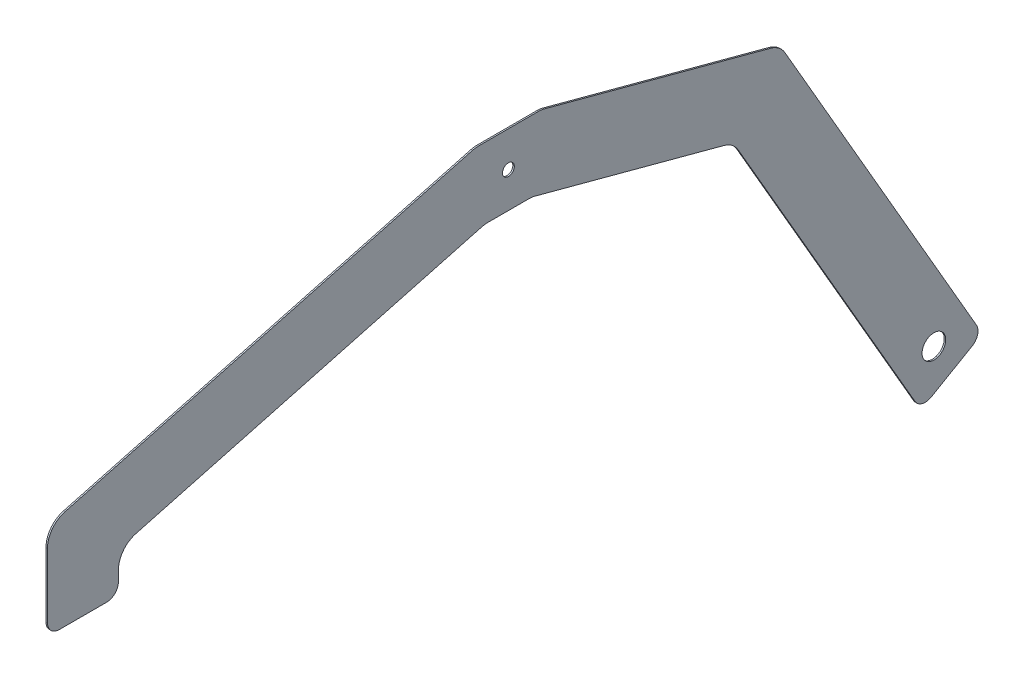
SolidWorks part; units mm, degrees
material "6061 Alloy"
ref_plane "Front Plane" through (0, 0, 0) normal (0, 0, 1) x (1, 0, 0)
ref_plane "Top Plane" through (0, 0, 0) normal (0, 1, 0) x (1, 0, 0)
ref_plane "Right Plane" through (0, 0, 0) normal (1, 0, 0) x (0, 0, -1)
sketch "Sketch1" plane through (0, 0, 0) normal (1, 0, 0) x (0, 0, -1)
  line L11 (-35.4319, 38.1) -> (35.4319, 38.1)
  line L12 (-25.4, -38.1) -> (25.4, -38.1)
  line L13 (0, -38.1) -> (0, 0) construction
  line L17 (-35.4319, 38.1) -> (-495.3, -85.1213)
  line L18 (-25.4, -38.1) -> (-419.1, -143.5916)
  line L19 (-495.3, -85.1213) -> (-495.3, -186.7213)
  line L20 (-495.3, -186.7213) -> (-419.1, -186.7213)
  line L21 (-419.1, -186.7213) -> (-419.1, -143.5916)
  line L22 (35.4319, 38.1) -> (291.9219, -30.6263)
  line L23 (25.4, -38.1) -> (241.7123, -96.0607)
  line L24 (241.7123, -96.0607) -> (443.2544, -445.1418)
  line L25 (443.2544, -445.1418) -> (509.2456, -407.0418)
  line L26 (509.2456, -407.0418) -> (291.9219, -30.6263)
  circle A0 centre (0, 0) radius 6.35
  circle A1 centre (457.2, -393.0963) radius 12.7
  point P9 (0, 0)
  point P18 (-457.2, -186.7213)
  dimension "D1" = 12.7
  dimension "D13" = 25.4
  dimension "D2" = 76.2
  dimension "D3" = 50.8
  dimension "D4" = 914.4
  dimension "D5" = 76.2
  dimension "D6" = 15
  dimension "D7" = 38.1
  dimension "D8" = 38.1
  dimension "D9" = 206.375
  dimension "D10" = 101.6
  dimension "D11" = 76.2
  dimension "D12" = 457.2
  dimension "D14" = 76.2
  dimension "D15" = 38.1
  dimension "D16" = 38.1
  dimension "D17" = 15
  dimension "D18" = 45
extrude "Boss-Extrude1" add sketch "Sketch1" along normal blind 1.5875
fillet "Fillet1" radius 25.4 1 edges at (0.7937, -85.1213, 495.3)
fillet "Fillet2" radius 25.4 1 edges at (0.7937, -143.5916, 419.1)
fillet "Fillet3" radius 25.4 3 edges at (0.7937, -96.0607, -241.7123) (0.7937, -38.1, -25.4) (0.7937, -38.1, 25.4)
fillet "Fillet4" radius 25.4 3 edges at (0.7937, 38.1, 35.4319) (0.7937, 38.1, -35.4319) (0.7937, -30.6263, -291.9219)
fillet "Fillet5" radius 12.7 4 edges at (0.7937, -407.0418, -509.2456) (0.7937, -445.1418, -443.2544) (0.7937, -186.7213, 419.1) (0.7937, -186.7213, 495.3)
